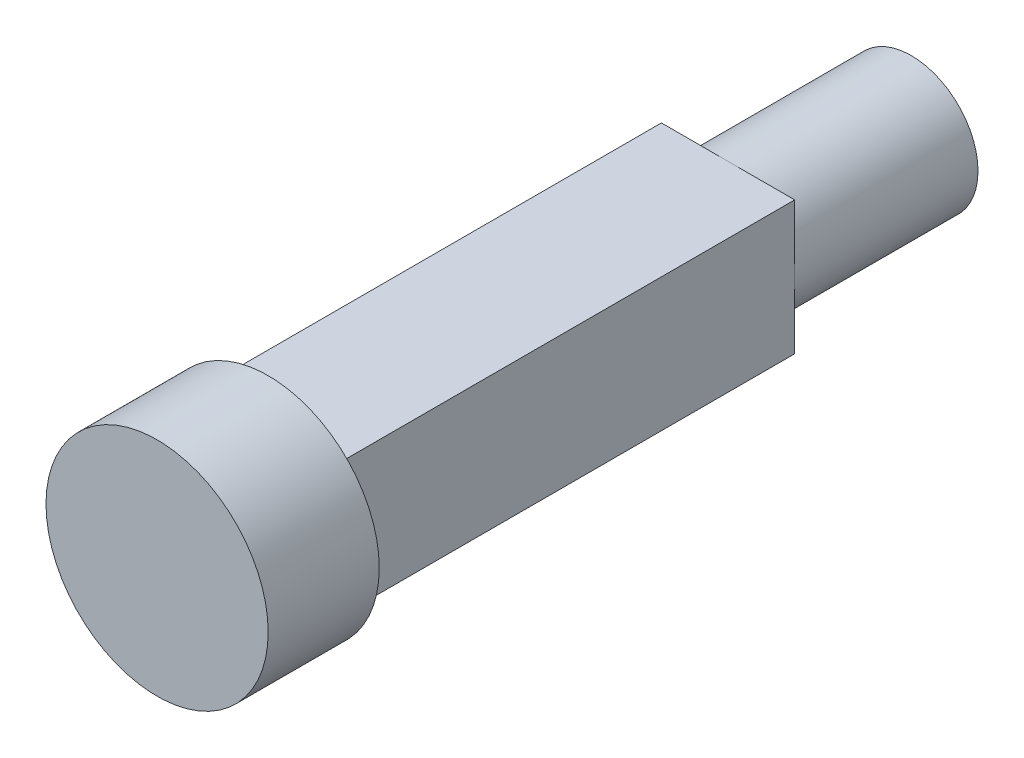
SolidWorks part; units mm, degrees
other "Marquage1"
sketch "Esquisse7" plane through (-5, -5, -40) normal (-1, 0, 0) x (0, 0, 1)
material "PLA"
ref_plane "Front Plane" through (0, 0, 0) normal (0, 0, 1) x (1, 0, 0)
ref_plane "Top Plane" through (0, 0, 0) normal (0, 1, 0) x (1, 0, 0)
ref_plane "Right Plane" through (0, 0, 0) normal (1, 0, 0) x (0, 0, -1)
sketch "Esquisse2" plane through (0, 0, 0) normal (1, 0, 0) x (0, 0, -1)
  line L0 (0, 0) -> (33.95, 0) construction
  line L1 (0, 0) -> (33.95, 0)
  line L4 (33.95, 0) -> (33.95, 3)
  line L5 (5, 3) -> (33.95, 3)
  line L9 (0, 5) -> (5, 5)
  line L10 (5, 3) -> (5, 5)
  line L11 (0, 5) -> (0, 0)
  line L14 (42.535, 0) -> (-4.8431, 0) construction
  dimension "D1" = 6
  dimension "D2" = 5
  dimension "D3" = 28.95
  dimension "D4" = 10
revolve "Révolution1" add sketch "Esquisse2" angle 360 about L0
sketch "Esquisse6" plane through (0, 0, -5) normal (0, 0, -1) x (-1, 0, 0)
  line L1 (-3, -3) -> (3, -3)
  line L2 (-3, -3) -> (-3, 3)
  line L3 (-3, 3) -> (3, 3)
  line L4 (3, -3) -> (3, 3)
  line L5 (-3, -3) -> (3, 3) construction
  line L6 (-3, 3) -> (3, -3) construction
  circle A0 centre (0, 0) radius 3 construction
  point P0 (0, 0)
extrude "Boss.-Extru.2" add sketch "Esquisse6" along normal blind 20.7
sketch "Esquisse4" plane through (0, 0, -33.95) normal (0, 0, -1) x (-1, 0, 0)
  line L0 (-1.2042, 1.2) -> (1.2042, 1.2)
  arc A0 (-1.2042, 1.2) -> (1.2042, 1.2) centre (0, 0) ccw
  dimension "D1" = 3.4
  dimension "D2" = 1.2
extrude "Enlèv. mat.-Extru.1" cut sketch "Esquisse4" against normal blind 10
